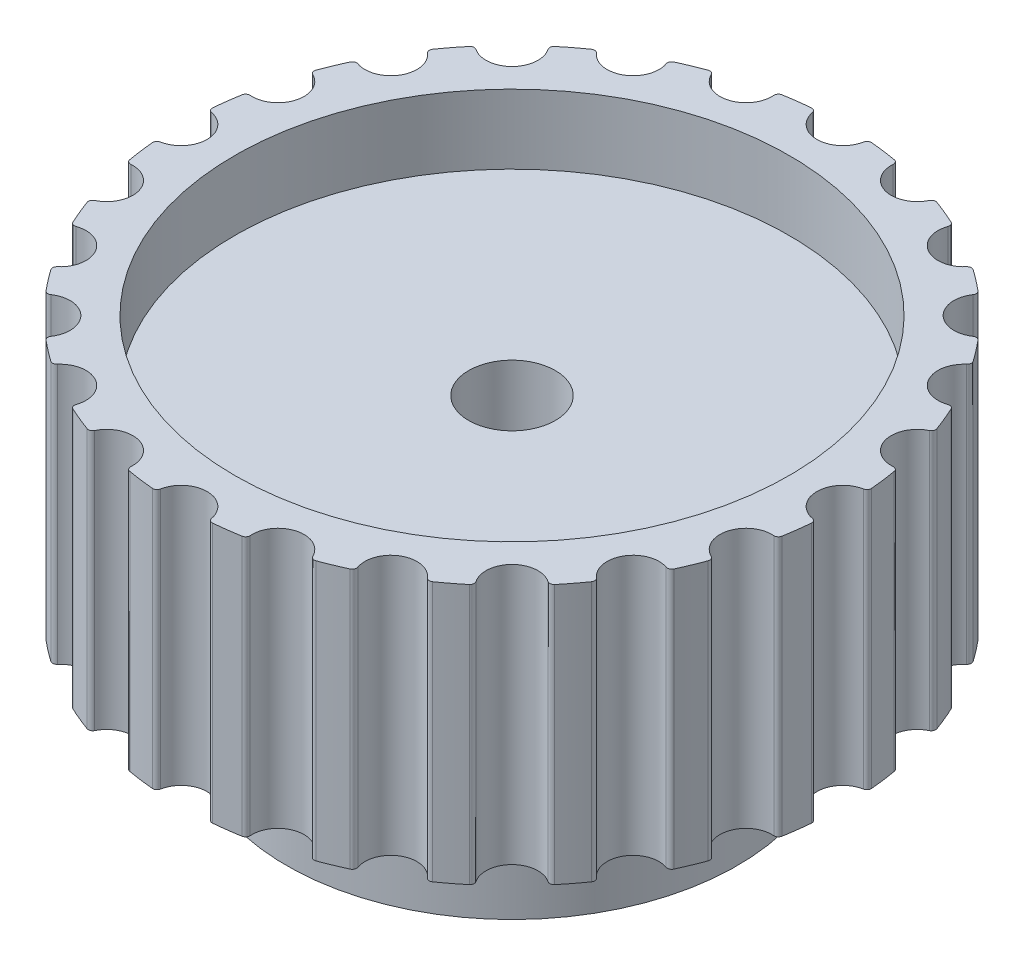
SolidWorks part; units mm, degrees
ref_plane "Front Plane" through (0, 0, 0) normal (0, 0, 1) x (1, 0, 0)
ref_plane "Top Plane" through (0, 0, 0) normal (0, 1, 0) x (1, 0, 0)
ref_plane "Right Plane" through (0, 0, 0) normal (1, 0, 0) x (0, 0, -1)
sketch "Sketch1" plane through (0, 0, 0) normal (0, 1, 0) x (1, 0, 0)
  circle A0 centre (0, 0) radius 19.095
  dimension "D1" = 38.19
extrude "Boss-Extrude1" add sketch "Sketch1" along normal blind 15
ref_plane "Plane1" through (0, 7.5, 0) normal (0, 1, 0) x (1, 0, 0)
sketch "Sketch2" plane through (0, 15, 0) normal (0, 1, 0) x (1, 0, 0)
  circle A0 centre (0, 0) radius 16
  dimension "D1" = 32
extrude "Cut-Extrude1" cut sketch "Sketch2" against normal blind 4
mirror "Mirror1" about plane through (0, 7.5, 0) normal (0, 1, 0) of "Cut-Extrude1"
sketch "Sketch4" plane through (0, 0, 0) normal (0, -1, 0) x (1, 0, 0)
  line L0 (0, 0) -> (0, 19.095) construction
  circle A0 centre (0, 0) radius 19.095 construction
  circle A1 centre (0, 19.095) radius 1.5
  dimension "D1" = 3
extrude "Cut-Extrude2" cut sketch "Sketch4" against normal through all
pattern_circular "CirPattern1" count 24 over 360 about axis through (0, 0, 0) along (0, 1, 0) of "Cut-Extrude2"
fillet "Fillet1" radius 0.25 48 edges at (6.3747, 7.5, 17.9995) (3.4791, 7.5, 18.7754) (10.8161, 7.5, 15.7363) (8.22, 7.5, 17.2352) (14.5204, 7.5, 12.4007) (12.4007, 7.5, 14.5204) (17.2352, 7.5, 8.22) (15.7363, 7.5, 10.8161) (18.7754, 7.5, 3.4791) (17.9995, 7.5, 6.3747) (19.0361, 7.5, -1.4988) (19.0361, 7.5, 1.4988) (17.9995, 7.5, -6.3747) (18.7754, 7.5, -3.4791) (15.7363, 7.5, -10.8161) (17.2352, 7.5, -8.22) (12.4007, 7.5, -14.5204) (14.5204, 7.5, -12.4007) (8.22, 7.5, -17.2352) (10.8161, 7.5, -15.7363) (3.4791, 7.5, -18.7754) (6.3747, 7.5, -17.9995) (-1.4988, 7.5, -19.0361) (1.4988, 7.5, -19.0361) (-6.3747, 7.5, -17.9995) (-3.4791, 7.5, -18.7754) (-10.8161, 7.5, -15.7363) (-8.22, 7.5, -17.2352) (-14.5204, 7.5, -12.4007) (-12.4007, 7.5, -14.5204) (-17.2352, 7.5, -8.22) (-15.7363, 7.5, -10.8161) (-18.7754, 7.5, -3.4791) (-17.9995, 7.5, -6.3747) (-19.0361, 7.5, 1.4988) (-19.0361, 7.5, -1.4988) (-17.9995, 7.5, 6.3747) (-18.7754, 7.5, 3.4791) (-15.7363, 7.5, 10.8161) (-17.2352, 7.5, 8.22) (-12.4007, 7.5, 14.5204) (-14.5204, 7.5, 12.4007) (-8.22, 7.5, 17.2352) (-10.8161, 7.5, 15.7363) (-3.4791, 7.5, 18.7754) (-6.3747, 7.5, 17.9995) (1.4988, 7.5, 19.0361) (-1.4988, 7.5, 19.0361)
sketch "Sketch5" plane through (0, 4, 0) normal (0, -1, 0) x (1, 0, 0)
  circle A0 centre (0, 0) radius 13
  dimension "D1" = 26
extrude "Boss-Extrude2" add sketch "Sketch5" along normal blind 10
sketch "Sketch6" plane through (0, -6, 0) normal (0, -1, 0) x (1, 0, 0)
  circle A0 centre (0, 0) radius 6
  dimension "D1" = 12
extrude "Cut-Extrude3" [suppressed] cut sketch "Sketch6" against normal through all
sketch "Sketch7" plane through (0, -6, 0) normal (0, -1, 0) x (1, 0, 0)
  circle A0 centre (0, 0) radius 2.5
  dimension "D1" = 5
extrude "Cut-Extrude4" cut sketch "Sketch7" against normal through all
